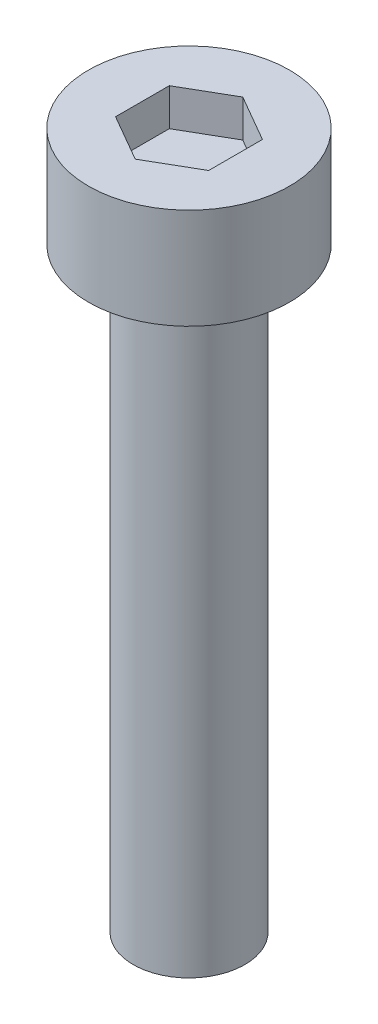
SolidWorks part; units mm, degrees
ref_plane "Front Plane" through (0, 0, 0) normal (0, 0, 1) x (1, 0, 0)
ref_plane "Top Plane" through (0, 0, 0) normal (0, 1, 0) x (1, 0, 0)
ref_plane "Right Plane" through (0, 0, 0) normal (1, 0, 0) x (0, 0, -1)
sketch "Sketch1" plane through (0, 0, 0) normal (0, 1, 0) x (1, 0, 0)
  circle A0 centre (0, 0) radius 2.7
extrude "Boss-Extrude1" add sketch "Sketch1" along normal blind 2.7
sketch "Sketch2" plane through (0, 2.7, 0) normal (0, 1, 0) x (1, 0, 0)
  line L1 (0, 1.4434) -> (-1.25, 0.7217)
  line L2 (-1.25, 0.7217) -> (-1.25, -0.7217)
  line L3 (-1.25, -0.7217) -> (0, -1.4434)
  line L4 (0, -1.4434) -> (1.25, -0.7217)
  line L5 (1.25, -0.7217) -> (1.25, 0.7217)
  line L6 (1.25, 0.7217) -> (0, 1.4434)
  circle A0 centre (0, 0) radius 1.25 construction
extrude "Cut-Extrude1" cut sketch "Sketch2" against normal blind 1
sketch "Sketch3" plane through (0, 0, 0) normal (0, -1, 0) x (1, 0, 0)
  circle A0 centre (0, 0) radius 1.5
extrude "Boss-Extrude2" add sketch "Sketch3" along normal blind 16
